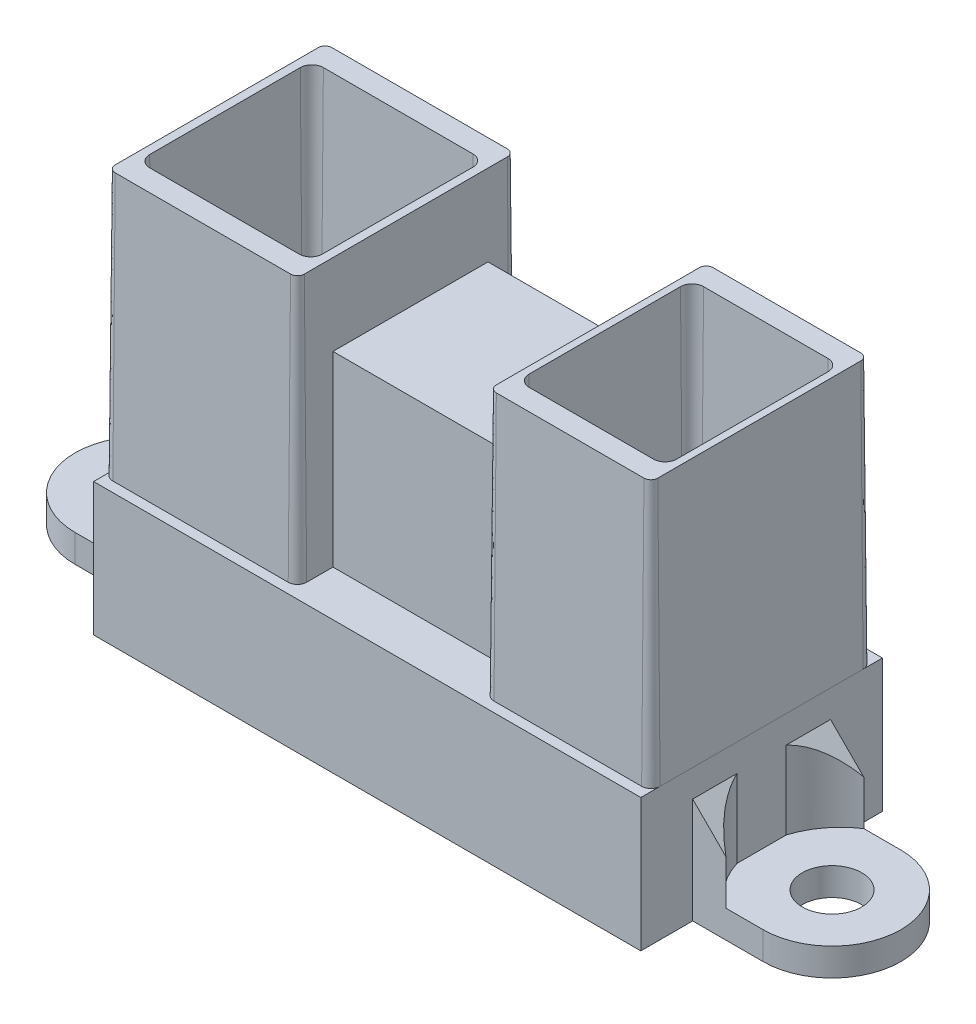
SolidWorks part; units mm, degrees
material "ABS"
ref_plane "Front Plane" through (0, 0, 0) normal (0, 0, 1) x (1, 0, 0)
ref_plane "Top Plane" through (0, 0, 0) normal (0, 1, 0) x (1, 0, 0)
ref_plane "Right Plane" through (0, 0, 0) normal (1, 0, 0) x (0, 0, -1)
sketch "Sketch1" plane through (0, 0, 0) normal (0, 1, 0) x (1, 0, 0)
  line L0 (-14.055, 5.775) -> (-5.355, 5.775)
  line L1 (-14.825, -6.545) -> (14.825, -6.545)
  line L2 (-14.825, -6.545) -> (-14.825, 6.545)
  line L3 (-14.825, 6.545) -> (-5.355, 6.545)
  line L4 (14.825, -6.545) -> (14.825, 6.545)
  line L5 (-14.825, -6.545) -> (14.825, 6.545) construction
  line L6 (-14.825, 6.545) -> (14.825, -6.545) construction
  line L7 (14.055, -5.775) -> (14.055, 5.775)
  line L8 (-14.055, -5.775) -> (14.055, -5.775)
  line L9 (-14.055, -5.775) -> (-14.055, 5.775)
  line L10 (0, 13.6604) -> (0, -14.8955) construction
  line L11 (-5.355, 6.545) -> (-5.355, 5.775)
  line L12 (5.355, 6.545) -> (5.355, 5.775)
  line L13 (5.355, 6.545) -> (14.825, 6.545)
  line L14 (-14.825, 6.545) -> (14.825, 6.545) construction
  line L15 (5.355, 5.775) -> (14.055, 5.775)
  line L16 (-14.055, 5.775) -> (14.055, 5.775) construction
  point P0 (0, 0)
  dimension "D1" = 29.65
  dimension "D2" = 13.09
  dimension "D3" = 0.77
  dimension "D4" = 5.355
extrude "Boss-Extrude1" add sketch "Sketch1" along normal blind 7.2
sketch "Sketch2" plane through (0, 0, 0) normal (0, 1, 0) x (1, 0, 0)
  line L0 (0, 11.5372) -> (0, -12.4354) construction
  line L1 (18.64, 3.735) -> (14.825, 3.735)
  line L2 (14.825, -6.545) -> (14.825, 6.545) construction
  line L3 (18.64, -3.735) -> (14.825, -3.735)
  line L4 (31.1664, 0) -> (-32.4313, 0) construction
  line L5 (14.825, 3.735) -> (14.825, -3.735)
  line L6 (-14.825, 3.735) -> (-14.825, -3.735)
  line L7 (-18.64, -3.735) -> (-14.825, -3.735)
  line L8 (-18.64, 3.735) -> (-14.825, 3.735)
  circle A0 centre (18.64, 0) radius 1.61
  arc A1 (18.64, -3.735) -> (18.64, 3.735) centre (18.64, 0) ccw
  arc A2 (-18.64, -3.735) -> (-18.64, 3.735) centre (-18.64, 0) cw
  circle A3 centre (-18.64, 0) radius 1.61
  point P12 (22.375, 0)
  point P20 (-22.375, 0)
  dimension "D1" = 3.22
  dimension "D2" = 7.47
  dimension "D3" = 7.55
extrude "Boss-Extrude2" add sketch "Sketch2" along normal blind 1.5
sketch "Sketch3" plane through (0, 7.2, 0) normal (0, 1, 0) x (1, 0, 0)
  line L1 (-14.825, -6.545) -> (14.825, -6.545)
  line L2 (-14.825, -6.545) -> (-14.825, 6.545)
  line L3 (-14.825, 6.545) -> (-5.355, 6.545)
  line L4 (14.825, -6.545) -> (14.825, 6.545)
  line L6 (-5.355, 5.775) -> (-5.355, 6.545) construction
  line L7 (-5.355, 6.545) -> (-5.355, 4.325)
  line L8 (-5.355, 4.325) -> (5.355, 4.325)
  line L9 (5.355, 6.545) -> (14.825, 6.545)
  line L10 (5.355, 4.325) -> (5.355, 6.545)
  dimension "D1" = 2.22
extrude "Boss-Extrude3" add sketch "Sketch3" against normal blind 0.7
sketch "Sketch4" plane through (0, 7.2, 0) normal (0, 1, 0) x (1, 0, 0)
  line L0 (-30.0342, 0) -> (29.9407, 0) construction
  line L1 (0, 17.7868) -> (0, -16.1974) construction
  line L2 (14.825, 3.735) -> (14.825, -3.735) construction
  line L3 (-14.325, -6) -> (-4.825, -6)
  line L4 (-14.825, -5.5) -> (-14.825, 5.5)
  line L5 (-14.325, 6) -> (-4.825, 6)
  line L6 (-4.325, -5.5) -> (-4.325, 5.5)
  line L7 (-14.825, -6) -> (-4.325, 6) construction
  line L8 (-14.825, 6) -> (-4.325, -6) construction
  line L9 (6.325, -6) -> (14.325, -6)
  line L10 (5.825, -5.5) -> (5.825, 5.5)
  line L11 (6.325, 6) -> (14.325, 6)
  line L12 (14.825, -5.5) -> (14.825, 5.5)
  line L13 (5.825, -6) -> (14.825, 6) construction
  line L14 (5.825, 6) -> (14.825, -6) construction
  line L15 (-14.825, 6.545) -> (-14.825, -6.545) construction
  line L17 (6.955, -4.6) -> (13.695, -4.6)
  line L18 (6.455, -4.1) -> (6.455, 4.1)
  line L19 (6.955, 4.6) -> (13.695, 4.6)
  line L20 (14.195, -4.1) -> (14.195, 4.1)
  line L21 (6.455, -4.6) -> (14.195, 4.6) construction
  line L22 (6.455, 4.6) -> (14.195, -4.6) construction
  line L23 (-13.625, -4.58) -> (-5.525, -4.58)
  line L24 (-14.125, -4.08) -> (-14.125, 4.08)
  line L25 (-13.625, 4.58) -> (-5.525, 4.58)
  line L26 (-5.025, -4.08) -> (-5.025, 4.08)
  line L27 (-14.125, -4.58) -> (-5.025, 4.58) construction
  line L28 (-14.125, 4.58) -> (-5.025, -4.58) construction
  arc A0 (6.325, -6) -> (5.825, -5.5) centre (6.325, -5.5) cw
  arc A1 (14.325, -6) -> (14.825, -5.5) centre (14.325, -5.5) ccw
  arc A2 (14.325, 6) -> (14.825, 5.5) centre (14.325, 5.5) cw
  arc A3 (5.825, 5.5) -> (6.325, 6) centre (6.325, 5.5) cw
  arc A4 (13.695, 4.6) -> (14.195, 4.1) centre (13.695, 4.1) cw
  arc A5 (13.695, -4.6) -> (14.195, -4.1) centre (13.695, -4.1) ccw
  arc A6 (6.955, -4.6) -> (6.455, -4.1) centre (6.955, -4.1) cw
  arc A7 (6.455, 4.1) -> (6.955, 4.6) centre (6.955, 4.1) cw
  arc A8 (-5.525, -4.58) -> (-5.025, -4.08) centre (-5.525, -4.08) ccw
  arc A9 (-5.525, 4.58) -> (-5.025, 4.08) centre (-5.525, 4.08) cw
  arc A10 (-14.125, 4.08) -> (-13.625, 4.58) centre (-13.625, 4.08) cw
  arc A11 (-13.625, -4.58) -> (-14.125, -4.08) centre (-13.625, -4.08) cw
  arc A12 (-14.325, -6) -> (-14.825, -5.5) centre (-14.325, -5.5) cw
  arc A13 (-4.825, -6) -> (-4.325, -5.5) centre (-4.825, -5.5) ccw
  arc A14 (-4.825, 6) -> (-4.325, 5.5) centre (-4.825, 5.5) cw
  arc A15 (-14.825, 5.5) -> (-14.325, 6) centre (-14.325, 5.5) cw
  point P1 (-9.575, 0)
  point P10 (10.325, 0)
  point P31 (10.325, 0)
  point P48 (-9.575, 0)
  dimension "D3" = 0.5
  dimension "D6" = 0.5
  dimension "D11" = 0.5
  dimension "D1" = 9
  dimension "D2" = 12
  dimension "D4" = 0.63
  dimension "D5" = 1.4
  dimension "D7" = 12
  dimension "D8" = 10.5
  dimension "D9" = 0.7
  dimension "D10" = 1.42
extrude "Boss-Extrude4" add sketch "Sketch4" along normal blind 14.4 draft 0.5
sketch "Sketch5" plane through (0, 7.2, 0) normal (0, 1, 0) x (1, 0, 0)
  line L0 (-4.325, -5.5) -> (-4.325, 4.325) construction
  line L1 (-4.325, 4.325) -> (5.825, 4.325)
  line L2 (-4.325, 4.325) -> (-4.325, -4.075)
  line L3 (-4.325, -4.075) -> (5.825, -4.075)
  line L4 (5.825, 4.325) -> (5.825, -4.075)
  line L6 (5.355, 4.325) -> (-4.325, 4.325) construction
  line L7 (5.825, 5.5) -> (5.825, -5.5) construction
  dimension "D1" = 8.4
extrude "Boss-Extrude5" add sketch "Sketch5" along normal blind 10.12
ref_plane "Plane1" through (0, 3.37, 0) normal (0, 1, 0) x (1, 0, 0)
sketch "Sketch6" plane through (0, 3.37, 0) normal (0, 1, 0) x (1, 0, 0)
  line L0 (5.825, 4.325) -> (-4.325, 4.325) construction
  line L1 (5.075, 9.825) -> (-5.075, 9.825)
  line L2 (5.075, 9.825) -> (5.075, 4.325)
  line L3 (5.075, 4.325) -> (-5.075, 4.325)
  line L4 (-5.075, 9.825) -> (-5.075, 4.325)
  line L5 (0, 19.7197) -> (0, -20.7995) construction
  point P7 (0, 9.825)
  dimension "D1" = 10.15
  dimension "D2" = 5.5
extrude "Boss-Extrude6" add sketch "Sketch6" along normal blind 6.35
sketch "Sketch7" plane through (0, 1.5, 0) normal (0, 1, 0) x (1, 0, 0)
  line L0 (-14.825, 3.735) -> (-16.625, 3.735)
  line L1 (-14.825, 3.735) -> (-18.64, 3.735) construction
  line L2 (-14.825, 3.735) -> (-14.825, 1.335)
  line L3 (-14.825, -3.735) -> (-14.825, 3.735) construction
  line L4 (-31.4685, 0) -> (3.2483, 0) construction
  line L5 (-14.825, -3.735) -> (-14.825, -1.335)
  line L6 (-14.825, -3.735) -> (-16.625, -3.735)
  line L7 (0, 19.5434) -> (0, -19.1533) construction
  line L8 (14.825, -3.735) -> (16.625, -3.735)
  line L9 (14.825, -3.735) -> (14.825, -1.335)
  line L10 (14.825, 3.735) -> (14.825, 1.335)
  line L11 (14.825, 3.735) -> (16.625, 3.735)
  arc A0 (-14.825, 1.335) -> (-16.625, 3.735) centre (-19.105, 0) ccw
  arc A1 (-14.825, -1.335) -> (-16.625, -3.735) centre (-19.105, 0) cw
  arc A2 (14.825, -1.335) -> (16.625, -3.735) centre (19.105, 0) ccw
  arc A3 (14.825, 1.335) -> (16.625, 3.735) centre (19.105, 0) cw
  dimension "D1" = 1.8
  dimension "D2" = 2.4
extrude "Boss-Extrude7" add sketch "Sketch7" along normal blind 4.22
sketch "Sketch8" plane through (0, 0, 0) normal (0, 0, 1) x (1, 0, 0)
  line L0 (-14.825, 5.72) -> (-16.625, 3.92)
  line L1 (-16.625, 5.72) -> (-16.625, 1.5) construction
  line L2 (0, 34.8249) -> (0, -17.4317) construction
  line L3 (14.825, 5.72) -> (16.625, 3.92)
  line L4 (-16.625, 5.72) -> (-14.825, 5.72) construction
  line L5 (-16.625, 3.92) -> (-16.625, 5.72)
  line L6 (-16.625, 5.72) -> (-14.825, 5.72)
  line L7 (16.625, 3.92) -> (16.625, 5.72)
  line L8 (16.625, 5.72) -> (14.825, 5.72)
  dimension "D1" = 45
extrude "Cut-Extrude1" cut sketch "Sketch8" against normal through all and the other way through all
sketch "Sketch9" plane through (0, 3.37, 0) normal (0, -1, 0) x (1, 0, 0)
  line L23 (14.055, 5.775) -> (14.055, -5.775) construction
  line L24 (-13.555, -5.275) -> (13.555, -5.275)
  line L25 (-13.555, -5.275) -> (-13.555, 5.275)
  line L26 (-13.555, 5.275) -> (13.555, 5.275)
  line L27 (13.555, -5.275) -> (13.555, 5.275)
  line L28 (-13.555, -5.275) -> (13.555, 5.275) construction
  line L29 (-13.555, 5.275) -> (13.555, -5.275) construction
  line L30 (14.055, 5.775) -> (-14.055, 5.775) construction
  point P6 (0, 0)
  dimension "D1" = 0.5
  dimension "D2" = 0.5
extrude "Boss-Extrude8" add sketch "Sketch9" against normal blind 1.2
